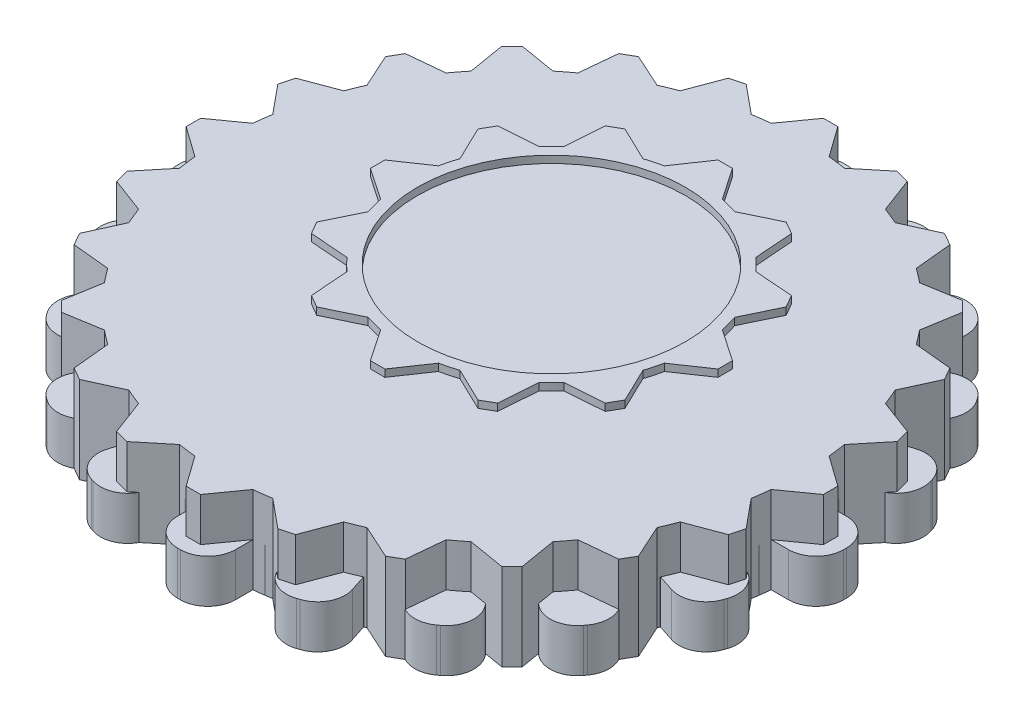
SolidWorks part; units mm, degrees
ref_plane "Front Plane" through (0, 0, 0) normal (0, 0, 1) x (1, 0, 0)
ref_plane "Top Plane" through (0, 0, 0) normal (0, 1, 0) x (1, 0, 0)
ref_plane "Right Plane" through (0, 0, 0) normal (1, 0, 0) x (0, 0, -1)
sketch "Sketch1" plane through (0, 0, 0) normal (0, 1, 0) x (1, 0, 0)
  line L86 (-2.6424, 4.8669) -> (1.3576, 4.8669)
  line L111 (-1.1424, 15.3669) -> (-0.1424, 15.3669)
  line L112 (-0.1424, 15.3669) -> (1.3576, 13.1649)
  line L113 (-1.1424, 15.3669) -> (-2.6424, 13.1649)
  line L114 (5.7906, 13.5092) -> (5.9886, 10.8522)
  line L115 (4.9246, 14.0092) -> (5.7906, 13.5092)
  line L116 (4.9246, 14.0092) -> (2.5245, 12.8522)
  line L117 (9.9999, 8.9339) -> (8.8429, 6.5338)
  line L118 (9.4999, 9.7999) -> (9.9999, 8.9339)
  line L119 (9.4999, 9.7999) -> (6.8429, 9.9979)
  line L120 (11.3576, 2.8669) -> (9.1556, 1.3669)
  line L121 (11.3576, 3.8669) -> (11.3576, 2.8669)
  line L122 (11.3576, 3.8669) -> (9.1556, 5.3669)
  line L123 (9.4999, -3.0661) -> (6.8429, -3.2641)
  line L124 (9.9999, -2.2001) -> (9.4999, -3.0661)
  line L125 (9.9999, -2.2001) -> (8.8429, 0.2)
  line L126 (4.9246, -7.2754) -> (2.5245, -6.1184)
  line L127 (5.7906, -6.7754) -> (4.9246, -7.2754)
  line L128 (5.7906, -6.7754) -> (5.9886, -4.1184)
  line L129 (-1.1424, -8.6331) -> (-2.6424, -6.4311)
  line L130 (-0.1424, -8.6331) -> (-1.1424, -8.6331)
  line L131 (-0.1424, -8.6331) -> (1.3576, -6.4311)
  line L132 (-7.0754, -6.7754) -> (-7.2734, -4.1184)
  line L133 (-6.2094, -7.2754) -> (-7.0754, -6.7754)
  line L134 (-6.2094, -7.2754) -> (-3.8093, -6.1184)
  line L135 (-11.2847, -2.2001) -> (-10.1277, 0.2)
  line L136 (-10.7847, -3.0661) -> (-11.2847, -2.2001)
  line L137 (-10.7847, -3.0661) -> (-8.1277, -3.2641)
  line L138 (-12.6424, 3.8669) -> (-10.4404, 5.3669)
  line L139 (-12.6424, 2.8669) -> (-12.6424, 3.8669)
  line L140 (-12.6424, 2.8669) -> (-10.4404, 1.3669)
  line L141 (-10.7847, 9.7999) -> (-8.1277, 9.9979)
  line L142 (-11.2847, 8.9339) -> (-10.7847, 9.7999)
  line L143 (-11.2847, 8.9339) -> (-10.1277, 6.5338)
  line L144 (-6.2094, 14.0092) -> (-3.8093, 12.8522)
  line L145 (-7.0754, 13.5092) -> (-6.2094, 14.0092)
  line L146 (-7.0754, 13.5092) -> (-7.2734, 10.8522)
  line L147 (-2.6424, 1.8669) -> (1.3576, 1.8669)
  line L149 (-3.1424, 4.8669) -> (1.8576, 1.8669) construction
  line L150 (-3.1424, 1.8669) -> (1.8576, 4.8669) construction
  arc A43 (-2.6424, 13.1649) -> (-3.8093, 12.8522) centre (-0.6424, 3.3669) ccw
  arc A44 (-7.2734, 10.8522) -> (-8.1277, 9.9979) centre (-0.6424, 3.3669) ccw
  arc A45 (-10.1277, 6.5338) -> (-10.4404, 5.3669) centre (-0.6424, 3.3669) ccw
  arc A46 (-10.4404, 1.3669) -> (-10.1277, 0.2) centre (-0.6424, 3.3669) ccw
  arc A47 (-8.1277, -3.2641) -> (-7.2734, -4.1184) centre (-0.6424, 3.3669) ccw
  arc A48 (-3.8093, -6.1184) -> (-2.6424, -6.4311) centre (-0.6424, 3.3669) ccw
  arc A49 (1.3576, -6.4311) -> (2.5245, -6.1184) centre (-0.6424, 3.3669) ccw
  arc A50 (5.9886, -4.1184) -> (6.8429, -3.2641) centre (-0.6424, 3.3669) ccw
  arc A51 (8.8429, 0.2) -> (9.1556, 1.3669) centre (-0.6424, 3.3669) ccw
  arc A52 (9.1556, 5.3669) -> (8.8429, 6.5338) centre (-0.6424, 3.3669) ccw
  arc A53 (6.8429, 9.9979) -> (5.9886, 10.8522) centre (-0.6424, 3.3669) ccw
  arc A54 (2.5245, 12.8522) -> (1.3576, 13.1649) centre (-0.6424, 3.3669) ccw
  arc A55 (-2.6424, 4.8669) -> (-2.6424, 1.8669) centre (-0.6424, 3.3669) ccw
  arc A56 (1.3576, 1.8669) -> (1.3576, 4.8669) centre (-0.6424, 3.3669) ccw
  point P6 (0, 0)
  point P8 (0, 0)
  point P9 (0, 0)
  point P12 (0, 2.7462)
  point P17 (0, 0)
  point P18 (0, 2.7462)
  point P22 (-2.5, 0.7462)
  point P63 (0, 0)
  point P68 (0, 0)
  point P69 (-0.6424, 3.3669)
  point P119 (0, 0)
  dimension "D1" = 20
  dimension "D2" = 3
  dimension "D3" = 5
  dimension "D8" = 12
sketch "Sketch2" plane through (0, 0, 0) normal (0, 1, 0) x (1, 0, 0)
  line L0 (-2, 0) -> (2, 0)
  line L1 (-23, -0.1) -> (-23, 0.1)
  line L2 (-21.1, 2) -> (-19.8997, 2)
  line L3 (-21.1, -2) -> (-19.8997, -2)
  line L4 (-20.6853, 4.6181) -> (-19.5438, 4.2472)
  line L5 (-19.4493, 8.4224) -> (-18.3078, 8.0515)
  line L6 (-21.9052, 7.0123) -> (-21.8434, 7.2025)
  line L7 (-18.2458, 10.7842) -> (-17.2748, 10.0787)
  line L8 (-15.8947, 14.0203) -> (-14.9237, 13.3148)
  line L9 (-18.6662, 13.4382) -> (-18.5486, 13.6)
  line L10 (-14.0203, 15.8947) -> (-13.3148, 14.9237)
  line L11 (-10.7842, 18.2458) -> (-10.0787, 17.2748)
  line L12 (-13.6, 18.5486) -> (-13.4382, 18.6662)
  line L13 (-8.4224, 19.4493) -> (-8.0515, 18.3078)
  line L14 (-4.6181, 20.6853) -> (-4.2472, 19.5438)
  line L15 (-7.2025, 21.8434) -> (-7.0123, 21.9052)
  line L16 (-2, 21.1) -> (-2, 19.8997)
  line L17 (2, 21.1) -> (2, 19.8997)
  line L18 (-0.1, 23) -> (0.1, 23)
  line L19 (4.6181, 20.6853) -> (4.2472, 19.5438)
  line L20 (8.4224, 19.4493) -> (8.0515, 18.3078)
  line L21 (7.0123, 21.9052) -> (7.2025, 21.8434)
  line L22 (10.7842, 18.2458) -> (10.0787, 17.2748)
  line L23 (14.0203, 15.8947) -> (13.3148, 14.9237)
  line L24 (13.4382, 18.6662) -> (13.6, 18.5486)
  line L25 (15.8947, 14.0203) -> (14.9237, 13.3148)
  line L26 (18.2458, 10.7842) -> (17.2748, 10.0787)
  line L27 (18.5486, 13.6) -> (18.6662, 13.4382)
  line L28 (19.4493, 8.4224) -> (18.3078, 8.0515)
  line L29 (20.6853, 4.6181) -> (19.5438, 4.2472)
  line L30 (21.8434, 7.2025) -> (21.9052, 7.0123)
  line L31 (21.1, 2) -> (19.8997, 2)
  line L32 (21.1, -2) -> (19.8997, -2)
  line L33 (23, 0.1) -> (23, -0.1)
  line L34 (20.6853, -4.6181) -> (19.5438, -4.2472)
  line L35 (19.4493, -8.4224) -> (18.3078, -8.0515)
  line L36 (21.9052, -7.0123) -> (21.8434, -7.2025)
  line L37 (18.2458, -10.7842) -> (17.2748, -10.0787)
  line L38 (15.8947, -14.0203) -> (14.9237, -13.3148)
  line L39 (18.6662, -13.4382) -> (18.5486, -13.6)
  line L40 (14.0203, -15.8947) -> (13.3148, -14.9237)
  line L41 (10.7842, -18.2458) -> (10.0787, -17.2748)
  line L42 (13.6, -18.5486) -> (13.4382, -18.6662)
  line L43 (8.4224, -19.4493) -> (8.0515, -18.3078)
  line L44 (4.6181, -20.6853) -> (4.2472, -19.5438)
  line L45 (7.2025, -21.8434) -> (7.0123, -21.9052)
  line L46 (2, -21.1) -> (2, -19.8997)
  line L47 (-2, -21.1) -> (-2, -19.8997)
  line L48 (0.1, -23) -> (-0.1, -23)
  line L49 (-4.6181, -20.6853) -> (-4.2472, -19.5438)
  line L50 (-8.4224, -19.4493) -> (-8.0515, -18.3078)
  line L51 (-7.0123, -21.9052) -> (-7.2025, -21.8434)
  line L52 (-10.7842, -18.2458) -> (-10.0787, -17.2748)
  line L53 (-14.0203, -15.8947) -> (-13.3148, -14.9237)
  line L54 (-13.4382, -18.6662) -> (-13.6, -18.5486)
  line L55 (-15.8947, -14.0203) -> (-14.9237, -13.3148)
  line L56 (-18.2458, -10.7842) -> (-17.2748, -10.0787)
  line L57 (-18.5486, -13.6) -> (-18.6662, -13.4382)
  line L58 (-19.4493, -8.4224) -> (-18.3078, -8.0515)
  line L59 (-20.6853, -4.6181) -> (-19.5438, -4.2472)
  line L60 (-21.8434, -7.2025) -> (-21.9052, -7.0123)
  arc A0 (-18.3078, -8.0515) -> (-17.2748, -10.0787) centre (0, 0) ccw
  arc A1 (-21.1, 2) -> (-23, 0.1) centre (-21.1, 0.1) ccw
  arc A2 (-21.1, -2) -> (-23, -0.1) centre (-21.1, -0.1) cw
  arc A3 (-20.6853, 4.6181) -> (-21.9052, 7.0123) centre (-20.0982, 6.4252) cw
  arc A4 (-19.4493, 8.4224) -> (-21.8434, 7.2025) centre (-20.0364, 6.6154) ccw
  arc A5 (-18.2458, 10.7842) -> (-18.6662, 13.4382) centre (-17.129, 12.3214) cw
  arc A6 (-15.8947, 14.0203) -> (-18.5486, 13.6) centre (-17.0115, 12.4832) ccw
  arc A7 (-14.0203, 15.8947) -> (-13.6, 18.5486) centre (-12.4832, 17.0115) cw
  arc A8 (-10.7842, 18.2458) -> (-13.4382, 18.6662) centre (-12.3214, 17.129) ccw
  arc A9 (-8.4224, 19.4493) -> (-7.2025, 21.8434) centre (-6.6154, 20.0364) cw
  arc A10 (-4.6181, 20.6853) -> (-7.0123, 21.9052) centre (-6.4252, 20.0982) ccw
  arc A11 (-2, 21.1) -> (-0.1, 23) centre (-0.1, 21.1) cw
  arc A12 (2, 21.1) -> (0.1, 23) centre (0.1, 21.1) ccw
  arc A13 (4.6181, 20.6853) -> (7.0123, 21.9052) centre (6.4252, 20.0982) cw
  arc A14 (8.4224, 19.4493) -> (7.2025, 21.8434) centre (6.6154, 20.0364) ccw
  arc A15 (10.7842, 18.2458) -> (13.4382, 18.6662) centre (12.3214, 17.129) cw
  arc A16 (14.0203, 15.8947) -> (13.6, 18.5486) centre (12.4832, 17.0115) ccw
  arc A17 (15.8947, 14.0203) -> (18.5486, 13.6) centre (17.0115, 12.4832) cw
  arc A18 (18.2458, 10.7842) -> (18.6662, 13.4382) centre (17.129, 12.3214) ccw
  arc A19 (19.4493, 8.4224) -> (21.8434, 7.2025) centre (20.0364, 6.6154) cw
  arc A20 (20.6853, 4.6181) -> (21.9052, 7.0123) centre (20.0982, 6.4252) ccw
  arc A21 (21.1, 2) -> (23, 0.1) centre (21.1, 0.1) cw
  arc A22 (21.1, -2) -> (23, -0.1) centre (21.1, -0.1) ccw
  arc A23 (20.6853, -4.6181) -> (21.9052, -7.0123) centre (20.0982, -6.4252) cw
  arc A24 (19.4493, -8.4224) -> (21.8434, -7.2025) centre (20.0364, -6.6154) ccw
  arc A25 (18.2458, -10.7842) -> (18.6662, -13.4382) centre (17.129, -12.3214) cw
  arc A26 (15.8947, -14.0203) -> (18.5486, -13.6) centre (17.0115, -12.4832) ccw
  arc A27 (14.0203, -15.8947) -> (13.6, -18.5486) centre (12.4832, -17.0115) cw
  arc A28 (10.7842, -18.2458) -> (13.4382, -18.6662) centre (12.3214, -17.129) ccw
  arc A29 (8.4224, -19.4493) -> (7.2025, -21.8434) centre (6.6154, -20.0364) cw
  arc A30 (4.6181, -20.6853) -> (7.0123, -21.9052) centre (6.4252, -20.0982) ccw
  arc A31 (2, -21.1) -> (0.1, -23) centre (0.1, -21.1) cw
  arc A32 (-2, -21.1) -> (-0.1, -23) centre (-0.1, -21.1) ccw
  arc A33 (-4.6181, -20.6853) -> (-7.0123, -21.9052) centre (-6.4252, -20.0982) cw
  arc A34 (-8.4224, -19.4493) -> (-7.2025, -21.8434) centre (-6.6154, -20.0364) ccw
  arc A35 (-10.7842, -18.2458) -> (-13.4382, -18.6662) centre (-12.3214, -17.129) cw
  arc A36 (-14.0203, -15.8947) -> (-13.6, -18.5486) centre (-12.4832, -17.0115) ccw
  arc A37 (-15.8947, -14.0203) -> (-18.5486, -13.6) centre (-17.0115, -12.4832) cw
  arc A38 (-18.2458, -10.7842) -> (-18.6662, -13.4382) centre (-17.129, -12.3214) ccw
  arc A39 (-19.4493, -8.4224) -> (-21.8434, -7.2025) centre (-20.0364, -6.6154) cw
  arc A40 (-20.6853, -4.6181) -> (-21.9052, -7.0123) centre (-20.0982, -6.4252) ccw
  arc A41 (-19.8997, -2) -> (-19.5438, -4.2472) centre (0, 0) ccw
  arc A42 (-19.5438, 4.2472) -> (-19.8997, 2) centre (0, 0) ccw
  arc A43 (-17.2748, 10.0787) -> (-18.3078, 8.0515) centre (0, 0) ccw
  arc A44 (-13.3148, 14.9237) -> (-14.9237, 13.3148) centre (0, 0) ccw
  arc A45 (-8.0515, 18.3078) -> (-10.0787, 17.2748) centre (0, 0) ccw
  arc A46 (-2, 19.8997) -> (-4.2472, 19.5438) centre (0, 0) ccw
  arc A47 (4.2472, 19.5438) -> (2, 19.8997) centre (0, 0) ccw
  arc A48 (10.0787, 17.2748) -> (8.0515, 18.3078) centre (0, 0) ccw
  arc A49 (14.9237, 13.3148) -> (13.3148, 14.9237) centre (0, 0) ccw
  arc A50 (18.3078, 8.0515) -> (17.2748, 10.0787) centre (0, 0) ccw
  arc A51 (19.8997, 2) -> (19.5438, 4.2472) centre (0, 0) ccw
  arc A52 (19.5438, -4.2472) -> (19.8997, -2) centre (0, 0) ccw
  arc A53 (17.2748, -10.0787) -> (18.3078, -8.0515) centre (0, 0) ccw
  arc A54 (13.3148, -14.9237) -> (14.9237, -13.3148) centre (0, 0) ccw
  arc A55 (8.0515, -18.3078) -> (10.0787, -17.2748) centre (0, 0) ccw
  arc A56 (2, -19.8997) -> (4.2472, -19.5438) centre (0, 0) ccw
  arc A57 (-10.0787, -17.2748) -> (-8.0515, -18.3078) centre (0, 0) ccw
  arc A58 (-4.2472, -19.5438) -> (-2, -19.8997) centre (0, 0) ccw
  arc A59 (-14.9237, -13.3148) -> (-13.3148, -14.9237) centre (0, 0) ccw
  point P6 (0, 0)
  point P10 (-23, 2)
  point P170 (0, 0)
  dimension "D1" = 40
  dimension "D4" = 1.9
  dimension "D5" = 20
extrude "Boss-Extrude3" add sketch "Sketch2" along normal blind 3
sketch "Sketch3" plane through (0, 0, 0) normal (0, 1, 0) x (1, 0, 0)
  line L0 (-22, 0) -> (22, 0)
  line L1 (22, -0.5) -> (22, 0.5)
  line L2 (22, 0.5) -> (19.8997, 2)
  line L3 (22, -0.5) -> (19.8997, -2)
  line L4 (21.3798, -5.2111) -> (19.7393, -3.2186)
  line L5 (21.121, -6.177) -> (21.3798, -5.2111)
  line L6 (21.121, -6.177) -> (18.704, -7.0823)
  line L7 (19.3026, -10.567) -> (18.2337, -8.2178)
  line L8 (18.8026, -11.433) -> (19.3026, -10.567)
  line L9 (18.8026, -11.433) -> (16.2337, -11.6819)
  line L10 (15.9099, -15.2028) -> (15.4855, -12.657)
  line L11 (15.2028, -15.9099) -> (15.9099, -15.2028)
  line L12 (15.2028, -15.9099) -> (12.657, -15.4855)
  line L13 (11.433, -18.8026) -> (11.6819, -16.2337)
  line L14 (10.567, -19.3026) -> (11.433, -18.8026)
  line L15 (10.567, -19.3026) -> (8.2178, -18.2337)
  line L16 (6.177, -21.121) -> (7.0823, -18.704)
  line L17 (5.2111, -21.3798) -> (6.177, -21.121)
  line L18 (5.2111, -21.3798) -> (3.2186, -19.7393)
  line L19 (0.5, -22) -> (2, -19.8997)
  line L20 (-0.5, -22) -> (0.5, -22)
  line L21 (-0.5, -22) -> (-2, -19.8997)
  line L22 (-5.2111, -21.3798) -> (-3.2186, -19.7393)
  line L23 (-6.177, -21.121) -> (-5.2111, -21.3798)
  line L24 (-6.177, -21.121) -> (-7.0823, -18.704)
  line L25 (-10.567, -19.3026) -> (-8.2178, -18.2337)
  line L26 (-11.433, -18.8026) -> (-10.567, -19.3026)
  line L27 (-11.433, -18.8026) -> (-11.6819, -16.2337)
  line L28 (-15.2028, -15.9099) -> (-12.657, -15.4855)
  line L29 (-15.9099, -15.2028) -> (-15.2028, -15.9099)
  line L30 (-15.9099, -15.2028) -> (-15.4855, -12.657)
  line L31 (-18.8026, -11.433) -> (-16.2337, -11.6819)
  line L32 (-19.3026, -10.567) -> (-18.8026, -11.433)
  line L33 (-19.3026, -10.567) -> (-18.2337, -8.2178)
  line L34 (-21.121, -6.177) -> (-18.704, -7.0823)
  line L35 (-21.3798, -5.2111) -> (-21.121, -6.177)
  line L36 (-21.3798, -5.2111) -> (-19.7393, -3.2186)
  line L37 (-22, -0.5) -> (-19.8997, -2)
  line L38 (-22, 0.5) -> (-22, -0.5)
  line L39 (-22, 0.5) -> (-19.8997, 2)
  line L40 (-21.3798, 5.2111) -> (-19.7393, 3.2186)
  line L41 (-21.121, 6.177) -> (-21.3798, 5.2111)
  line L42 (-21.121, 6.177) -> (-18.704, 7.0823)
  line L43 (-19.3026, 10.567) -> (-18.2337, 8.2178)
  line L44 (-18.8026, 11.433) -> (-19.3026, 10.567)
  line L45 (-18.8026, 11.433) -> (-16.2337, 11.6819)
  line L46 (-15.9099, 15.2028) -> (-15.4855, 12.657)
  line L47 (-15.2028, 15.9099) -> (-15.9099, 15.2028)
  line L48 (-15.2028, 15.9099) -> (-12.657, 15.4855)
  line L49 (-11.433, 18.8026) -> (-11.6819, 16.2337)
  line L50 (-10.567, 19.3026) -> (-11.433, 18.8026)
  line L51 (-10.567, 19.3026) -> (-8.2178, 18.2337)
  line L52 (-6.177, 21.121) -> (-7.0823, 18.704)
  line L53 (-5.2111, 21.3798) -> (-6.177, 21.121)
  line L54 (-5.2111, 21.3798) -> (-3.2186, 19.7393)
  line L55 (-0.5, 22) -> (-2, 19.8997)
  line L56 (0.5, 22) -> (-0.5, 22)
  line L57 (0.5, 22) -> (2, 19.8997)
  line L58 (5.2111, 21.3798) -> (3.2186, 19.7393)
  line L59 (6.177, 21.121) -> (5.2111, 21.3798)
  line L60 (6.177, 21.121) -> (7.0823, 18.704)
  line L61 (10.567, 19.3026) -> (8.2178, 18.2337)
  line L62 (11.433, 18.8026) -> (10.567, 19.3026)
  line L63 (11.433, 18.8026) -> (11.6819, 16.2337)
  line L64 (15.2028, 15.9099) -> (12.657, 15.4855)
  line L65 (15.9099, 15.2028) -> (15.2028, 15.9099)
  line L66 (15.9099, 15.2028) -> (15.4855, 12.657)
  line L67 (18.8026, 11.433) -> (16.2337, 11.6819)
  line L68 (19.3026, 10.567) -> (18.8026, 11.433)
  line L69 (19.3026, 10.567) -> (18.2337, 8.2178)
  line L70 (21.121, 6.177) -> (18.704, 7.0823)
  line L71 (21.3798, 5.2111) -> (21.121, 6.177)
  line L72 (21.3798, 5.2111) -> (19.7393, 3.2186)
  arc A0 (-8.2178, -18.2337) -> (-7.0823, -18.704) centre (0, 0) ccw
  arc A1 (-12.657, -15.4855) -> (-11.6819, -16.2337) centre (0, 0) ccw
  arc A2 (-16.2337, -11.6819) -> (-15.4855, -12.657) centre (0, 0) ccw
  arc A3 (-18.704, -7.0823) -> (-18.2337, -8.2178) centre (0, 0) ccw
  arc A4 (-19.8997, -2) -> (-19.7393, -3.2186) centre (0, 0) ccw
  arc A5 (-19.7393, 3.2186) -> (-19.8997, 2) centre (0, 0) ccw
  arc A6 (-18.2337, 8.2178) -> (-18.704, 7.0823) centre (0, 0) ccw
  arc A7 (-15.4855, 12.657) -> (-16.2337, 11.6819) centre (0, 0) ccw
  arc A8 (-11.6819, 16.2337) -> (-12.657, 15.4855) centre (0, 0) ccw
  arc A9 (-7.0823, 18.704) -> (-8.2178, 18.2337) centre (0, 0) ccw
  arc A10 (-2, 19.8997) -> (-3.2186, 19.7393) centre (0, 0) ccw
  arc A11 (3.2186, 19.7393) -> (2, 19.8997) centre (0, 0) ccw
  arc A12 (8.2178, 18.2337) -> (7.0823, 18.704) centre (0, 0) ccw
  arc A13 (12.657, 15.4855) -> (11.6819, 16.2337) centre (0, 0) ccw
  arc A14 (16.2337, 11.6819) -> (15.4855, 12.657) centre (0, 0) ccw
  arc A15 (18.704, 7.0823) -> (18.2337, 8.2178) centre (0, 0) ccw
  arc A16 (19.8997, 2) -> (19.7393, 3.2186) centre (0, 0) ccw
  arc A17 (19.7393, -3.2186) -> (19.8997, -2) centre (0, 0) ccw
  arc A18 (18.2337, -8.2178) -> (18.704, -7.0823) centre (0, 0) ccw
  arc A19 (-3.2186, -19.7393) -> (-2, -19.8997) centre (0, 0) ccw
  arc A20 (2, -19.8997) -> (3.2186, -19.7393) centre (0, 0) ccw
  arc A21 (7.0823, -18.704) -> (8.2178, -18.2337) centre (0, 0) ccw
  arc A22 (11.6819, -16.2337) -> (12.657, -15.4855) centre (0, 0) ccw
  arc A23 (15.4855, -12.657) -> (16.2337, -11.6819) centre (0, 0) ccw
  point P6 (0, 0)
  point P7 (0, -12.952)
  point P8 (-6.2727, 0)
  point P9 (11.4668, 0)
  point P10 (0, 0)
  point P108 (0, 0)
  dimension "D1" = 40
  dimension "D2" = 22
  dimension "D3" = 2
  dimension "D4" = 24
extrude "Boss-Extrude5" add sketch "Sketch3" along normal blind 6 separate body contours L2 A16 L72 L71 L70 A15 L69 L68 L67 A14 L66 L65 L64 A13 L63 L62 L61 A12 L60 L59 L58 A11 L57 L56 L55 A10 L54 L53 L52 A9 L51 L50 L49 A8 L48 L47 L46 A7 L45 L44 L43 A6 L42 L41 L40 A5 L39 L38 L0 L1 | L10 A23 L9 L8 L7 A18 L6 L5 L4 A17 L3 L1 L0 L38 L37 A4 L36 L35 L34 A3 L33 L32 L31 A2 L30 L29 L28 A1 L27 L26 L25 A0 L24 L23 L22 A19 L21 L20 L19 A20 L18 L17 L16 A21 L15 L14 L13 A22 L12 L11
extrude "Boss-Extrude6" add sketch "Sketch1" along normal blind 5 separate body
sketch "Sketch5" plane through (0, 5, 0) normal (0, 1, 0) x (1, 0, 0)
  line L0 (-0.6424, 15.3669) -> (-0.6424, -8.6331) construction
  line L1 (-0.1424, 15.3669) -> (-1.1424, 15.3669) construction
  line L2 (-1.1424, -8.6331) -> (-0.1424, -8.6331) construction
  line L3 (11.3576, 3.3669) -> (-12.6424, 3.3669) construction
  line L4 (11.3576, 2.8669) -> (11.3576, 3.8669) construction
  line L5 (-12.6424, 3.8669) -> (-12.6424, 2.8669) construction
  circle A0 centre (-0.6424, 3.3669) radius 5.1751
sketch "Sketch6" plane through (0, 5, 0) normal (0, 1, 0) x (1, 0, 0)
  line L72 (-1.1424, 15.3669) -> (-2.6424, 13.1649)
  line L73 (-3.8093, 12.8522) -> (-6.2094, 14.0092)
  line L74 (-6.2094, 14.0092) -> (-7.0754, 13.5092)
  line L75 (-7.0754, 13.5092) -> (-7.2734, 10.8522)
  line L76 (-8.1277, 9.9979) -> (-10.7847, 9.7999)
  line L77 (-10.7847, 9.7999) -> (-11.2847, 8.9339)
  line L78 (-11.2847, 8.9339) -> (-10.1277, 6.5338)
  line L79 (-10.4404, 5.3669) -> (-12.6424, 3.8669)
  line L80 (-12.6424, 3.8669) -> (-12.6424, 2.8669)
  line L81 (-12.6424, 2.8669) -> (-10.4404, 1.3669)
  line L82 (-10.1277, 0.2) -> (-11.2847, -2.2001)
  line L83 (-11.2847, -2.2001) -> (-10.7847, -3.0661)
  line L84 (-10.7847, -3.0661) -> (-8.1277, -3.2641)
  line L85 (-7.2734, -4.1184) -> (-7.0754, -6.7754)
  line L86 (-7.0754, -6.7754) -> (-6.2094, -7.2754)
  line L87 (-6.2094, -7.2754) -> (-3.8093, -6.1184)
  line L88 (-2.6424, -6.4311) -> (-1.1424, -8.6331)
  line L89 (-1.1424, -8.6331) -> (-0.1424, -8.6331)
  line L90 (-0.1424, -8.6331) -> (1.3576, -6.4311)
  line L91 (2.5245, -6.1184) -> (4.9246, -7.2754)
  line L92 (4.9246, -7.2754) -> (5.7906, -6.7754)
  line L93 (5.7906, -6.7754) -> (5.9886, -4.1184)
  line L94 (6.8429, -3.2641) -> (9.4999, -3.0661)
  line L95 (9.4999, -3.0661) -> (9.9999, -2.2001)
  line L96 (9.9999, -2.2001) -> (8.8429, 0.2)
  line L97 (9.1556, 1.3669) -> (11.3576, 2.8669)
  line L98 (11.3576, 2.8669) -> (11.3576, 3.8669)
  line L99 (11.3576, 3.8669) -> (9.1556, 5.3669)
  line L100 (8.8429, 6.5338) -> (9.9999, 8.9339)
  line L101 (9.9999, 8.9339) -> (9.4999, 9.7999)
  line L102 (9.4999, 9.7999) -> (6.8429, 9.9979)
  line L103 (5.9886, 10.8522) -> (5.7906, 13.5092)
  line L104 (5.7906, 13.5092) -> (4.9246, 14.0092)
  line L105 (4.9246, 14.0092) -> (2.5245, 12.8522)
  line L106 (1.3576, 13.1649) -> (-0.1424, 15.3669)
  line L107 (-0.1424, 15.3669) -> (-1.1424, 15.3669)
  line L108 (-1.1424, 15.3669) -> (-2.6424, 13.1649)
  line L109 (-3.8093, 12.8522) -> (-6.2094, 14.0092)
  line L110 (-6.2094, 14.0092) -> (-7.0754, 13.5092)
  line L111 (-7.0754, 13.5092) -> (-7.2734, 10.8522)
  line L112 (-8.1277, 9.9979) -> (-10.7847, 9.7999)
  line L113 (-10.7847, 9.7999) -> (-11.2847, 8.9339)
  line L114 (-11.2847, 8.9339) -> (-10.1277, 6.5338)
  line L115 (-10.4404, 5.3669) -> (-12.6424, 3.8669)
  line L116 (-12.6424, 3.8669) -> (-12.6424, 2.8669)
  line L117 (-12.6424, 2.8669) -> (-10.4404, 1.3669)
  line L118 (-10.1277, 0.2) -> (-11.2847, -2.2001)
  line L119 (-11.2847, -2.2001) -> (-10.7847, -3.0661)
  line L120 (-10.7847, -3.0661) -> (-8.1277, -3.2641)
  line L121 (-7.2734, -4.1184) -> (-7.0754, -6.7754)
  line L122 (-7.0754, -6.7754) -> (-6.2094, -7.2754)
  line L123 (-6.2094, -7.2754) -> (-3.8093, -6.1184)
  line L124 (-2.6424, -6.4311) -> (-1.1424, -8.6331)
  line L125 (-1.1424, -8.6331) -> (-0.1424, -8.6331)
  line L126 (-0.1424, -8.6331) -> (1.3576, -6.4311)
  line L127 (2.5245, -6.1184) -> (4.9246, -7.2754)
  line L128 (4.9246, -7.2754) -> (5.7906, -6.7754)
  line L129 (5.7906, -6.7754) -> (5.9886, -4.1184)
  line L130 (6.8429, -3.2641) -> (9.4999, -3.0661)
  line L131 (9.4999, -3.0661) -> (9.9999, -2.2001)
  line L132 (9.9999, -2.2001) -> (8.8429, 0.2)
  line L133 (9.1556, 1.3669) -> (11.3576, 2.8669)
  line L134 (11.3576, 2.8669) -> (11.3576, 3.8669)
  line L135 (11.3576, 3.8669) -> (9.1556, 5.3669)
  line L136 (8.8429, 6.5338) -> (9.9999, 8.9339)
  line L137 (9.9999, 8.9339) -> (9.4999, 9.7999)
  line L138 (9.4999, 9.7999) -> (6.8429, 9.9979)
  line L139 (5.9886, 10.8522) -> (5.7906, 13.5092)
  line L140 (5.7906, 13.5092) -> (4.9246, 14.0092)
  line L141 (4.9246, 14.0092) -> (2.5245, 12.8522)
  line L142 (1.3576, 13.1649) -> (-0.1424, 15.3669)
  line L143 (-0.1424, 15.3669) -> (-1.1424, 15.3669)
  circle A0 centre (-0.6424, 3.3669) radius 9.25
  arc A27 (-2.6424, 13.1649) -> (-3.8093, 12.8522) centre (-0.6424, 3.3669) ccw
  arc A28 (-7.2734, 10.8522) -> (-8.1277, 9.9979) centre (-0.6424, 3.3669) ccw
  arc A29 (-10.1277, 6.5338) -> (-10.4404, 5.3669) centre (-0.6424, 3.3669) ccw
  arc A30 (-10.4404, 1.3669) -> (-10.1277, 0.2) centre (-0.6424, 3.3669) ccw
  arc A31 (-8.1277, -3.2641) -> (-7.2734, -4.1184) centre (-0.6424, 3.3669) ccw
  arc A32 (-3.8093, -6.1184) -> (-2.6424, -6.4311) centre (-0.6424, 3.3669) ccw
  arc A33 (1.3576, -6.4311) -> (2.5245, -6.1184) centre (-0.6424, 3.3669) ccw
  arc A34 (5.9886, -4.1184) -> (6.8429, -3.2641) centre (-0.6424, 3.3669) ccw
  arc A35 (8.8429, 0.2) -> (9.1556, 1.3669) centre (-0.6424, 3.3669) ccw
  arc A36 (9.1556, 5.3669) -> (8.8429, 6.5338) centre (-0.6424, 3.3669) ccw
  arc A37 (6.8429, 9.9979) -> (5.9886, 10.8522) centre (-0.6424, 3.3669) ccw
  arc A38 (2.5245, 12.8522) -> (1.3576, 13.1649) centre (-0.6424, 3.3669) ccw
  arc A39 (-2.6424, 13.1649) -> (-3.8093, 12.8522) centre (-0.6424, 3.3669) ccw
  arc A40 (-7.2734, 10.8522) -> (-8.1277, 9.9979) centre (-0.6424, 3.3669) ccw
  arc A41 (-10.1277, 6.5338) -> (-10.4404, 5.3669) centre (-0.6424, 3.3669) ccw
  arc A42 (-10.4404, 1.3669) -> (-10.1277, 0.2) centre (-0.6424, 3.3669) ccw
  arc A43 (-8.1277, -3.2641) -> (-7.2734, -4.1184) centre (-0.6424, 3.3669) ccw
  arc A44 (-3.8093, -6.1184) -> (-2.6424, -6.4311) centre (-0.6424, 3.3669) ccw
  arc A45 (1.3576, -6.4311) -> (2.5245, -6.1184) centre (-0.6424, 3.3669) ccw
  arc A46 (5.9886, -4.1184) -> (6.8429, -3.2641) centre (-0.6424, 3.3669) ccw
  arc A47 (8.8429, 0.2) -> (9.1556, 1.3669) centre (-0.6424, 3.3669) ccw
  arc A48 (9.1556, 5.3669) -> (8.8429, 6.5338) centre (-0.6424, 3.3669) ccw
  arc A49 (6.8429, 9.9979) -> (5.9886, 10.8522) centre (-0.6424, 3.3669) ccw
  arc A50 (2.5245, 12.8522) -> (1.3576, 13.1649) centre (-0.6424, 3.3669) ccw
  dimension "D1" = 18.5
  dimension "D3" = 0
extrude "Boss-Extrude7" add sketch "Sketch6" along normal blind 1.5
